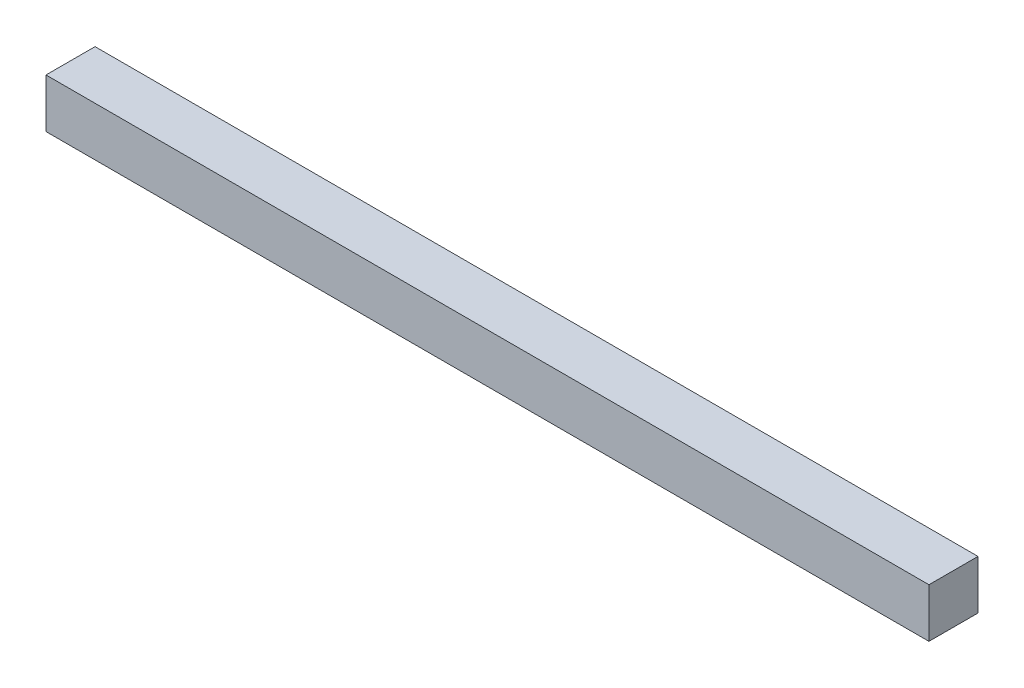
SolidWorks part; units mm, degrees
material "Alloy Steel"
ref_plane "Front Plane" through (0, 0, 0) normal (0, 0, 1) x (1, 0, 0)
ref_plane "Top Plane" through (0, 0, 0) normal (0, 1, 0) x (1, 0, 0)
ref_plane "Right Plane" through (0, 0, 0) normal (1, 0, 0) x (0, 0, -1)
sketch "Sketch2" plane through (0, 0, 0) normal (1, 0, 0) x (0, 0, -1)
  line L1 (3.175, -3.175) -> (-3.175, -3.175)
  line L2 (3.175, -3.175) -> (3.175, 3.175)
  line L3 (3.175, 3.175) -> (-3.175, 3.175)
  line L4 (-3.175, -3.175) -> (-3.175, 3.175)
  line L5 (3.175, -3.175) -> (-3.175, 3.175) construction
  line L6 (3.175, 3.175) -> (-3.175, -3.175) construction
  point P0 (0, 0)
  dimension "D1" = 6.35
  dimension "D2" = 6.35
extrude "Boss-Extrude1" add sketch "Sketch2" along normal mid plane 114.3
